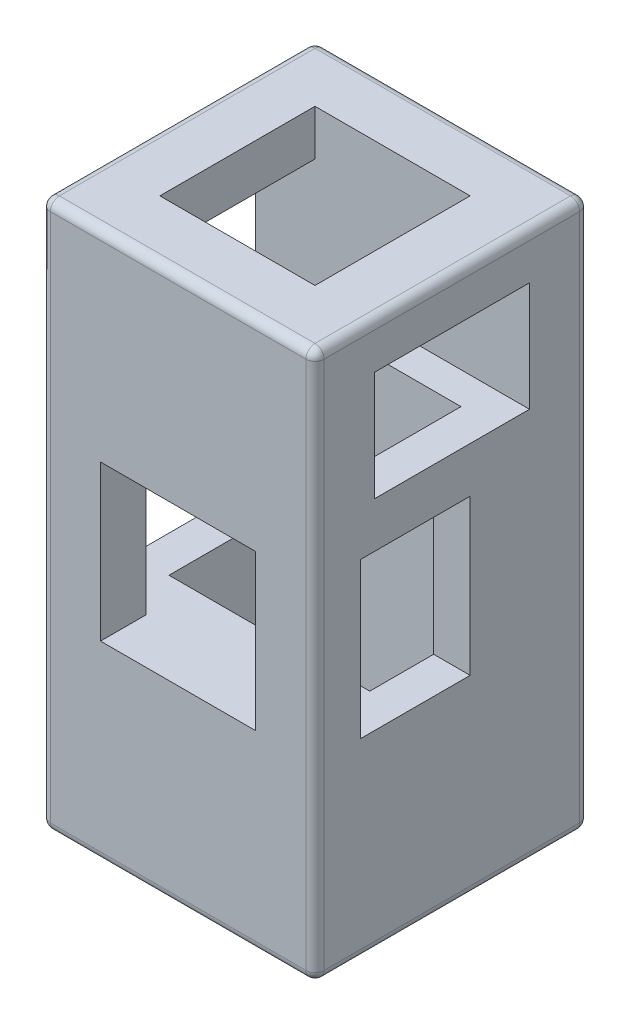
SolidWorks part; units mm, degrees
ref_plane "正面" through (0, 0, 0) normal (0, 0, 1) x (1, 0, 0)
ref_plane "平面" through (0, 0, 0) normal (0, 1, 0) x (1, 0, 0)
ref_plane "右側面" through (0, 0, 0) normal (1, 0, 0) x (0, 0, -1)
sketch "ｽｹｯﾁ1" plane through (0, 0, 0) normal (0, 1, 0) x (1, 0, 0)
  line L1 (-15, 15) -> (15, 15)
  line L2 (-15, 15) -> (-15, -15)
  line L3 (-15, -15) -> (15, -15)
  line L4 (15, 15) -> (15, -15)
  line L5 (-15, 15) -> (15, -15) construction
  line L6 (-15, -15) -> (15, 15) construction
  point P0 (0, 0)
  dimension "D1" = 30
  dimension "D2" = 30
extrude "ﾎﾞｽ - 押し出し2" add sketch "ｽｹｯﾁ1" along normal blind 60
sketch "ｽｹｯﾁ2" plane through (0, 0, 0) normal (0, -1, 0) x (1, 0, 0)
  line L1 (-11, 5) -> (11, 5)
  line L2 (-11, 5) -> (-11, -5)
  line L3 (-11, -5) -> (11, -5)
  line L4 (11, 5) -> (11, -5)
  line L5 (-11, 5) -> (11, -5) construction
  line L6 (-11, -5) -> (11, 5) construction
  point P0 (0, 0)
  dimension "D1" = 10
  dimension "D2" = 22
extrude "ｶｯﾄ - 押し出し1" cut sketch "ｽｹｯﾁ2" against normal blind 47
sketch "ｽｹｯﾁ3" plane through (15, 0, 0) normal (1, 0, 0) x (0, 0, -1)
  line L0 (-15, 60) -> (-15, 0) construction
  line L1 (-8.5, 43) -> (8.5, 43)
  line L2 (-8.5, 43) -> (-8.5, 55)
  line L3 (-8.5, 55) -> (8.5, 55)
  line L4 (8.5, 43) -> (8.5, 55)
  line L5 (-8.5, 43) -> (8.5, 55) construction
  line L6 (-8.5, 55) -> (8.5, 43) construction
  line L7 (15, 60) -> (-15, 60) construction
  point P0 (0, 49)
  dimension "D1" = 12
  dimension "D2" = 17
  dimension "D3" = 15
  dimension "D4" = 5
extrude "ｶｯﾄ - 押し出し2" cut sketch "ｽｹｯﾁ3" against normal through all
sketch "ｽｹｯﾁ5" plane through (0, 60, 0) normal (0, 1, 0) x (1, 0, 0)
  line L1 (8.5, -8.5) -> (-8.5, -8.5)
  line L2 (8.5, -8.5) -> (8.5, 8.5)
  line L3 (8.5, 8.5) -> (-8.5, 8.5)
  line L4 (-8.5, -8.5) -> (-8.5, 8.5)
  line L5 (8.5, -8.5) -> (-8.5, 8.5) construction
  line L6 (8.5, 8.5) -> (-8.5, -8.5) construction
  point P0 (0, 0)
  dimension "D1" = 17
  dimension "D2" = 17
extrude "ｶｯﾄ - 押し出し3" cut sketch "ｽｹｯﾁ5" against normal blind 5
sketch "ｽｹｯﾁ6" plane through (15, 0, 0) normal (1, 0, 0) x (0, 0, -1)
  line L0 (-15, 60) -> (-15, 0) construction
  line L1 (2, 38) -> (-10, 38)
  line L2 (2, 38) -> (2, 21)
  line L3 (2, 21) -> (-10, 21)
  line L4 (-10, 38) -> (-10, 21)
  line L5 (2, 38) -> (-10, 21) construction
  line L6 (2, 21) -> (-10, 38) construction
  line L7 (-8.5, 43) -> (8.5, 43) construction
  point P0 (-4, 29.5)
  dimension "D1" = 17
  dimension "D2" = 12
  dimension "D3" = 5
  dimension "D4" = 5
extrude "ｶｯﾄ - 押し出し4" cut sketch "ｽｹｯﾁ6" against normal through all
sketch "ｽｹｯﾁ7" plane through (0, 0, 15) normal (0, 0, 1) x (1, 0, 0)
  line L0 (15, 60) -> (15, 0) construction
  line L1 (-8.5, 38) -> (8.5, 38)
  line L2 (-8.5, 38) -> (-8.5, 21)
  line L3 (-8.5, 21) -> (8.5, 21)
  line L4 (8.5, 38) -> (8.5, 21)
  line L5 (-8.5, 38) -> (8.5, 21) construction
  line L6 (-8.5, 21) -> (8.5, 38) construction
  line L8 (-15, 60) -> (15, 60) construction
  point P0 (0, 29.5)
  dimension "D1" = 17
  dimension "D2" = 17
  dimension "D3" = 15
  dimension "D4" = 22
extrude "ｶｯﾄ - 押し出し5" cut sketch "ｽｹｯﾁ7" against normal blind 5
fillet "ﾌｨﾚｯﾄ1" radius 1 1 edges at (15, 30, 15)
fillet "ﾌｨﾚｯﾄ2" radius 1 3 edges at (15, 0, -0.5) (14.7071, 0, 14.7071) (-0.5, 0, 15)
fillet "ﾌｨﾚｯﾄ3" radius 1 3 edges at (15, 30.5, -15) (14.7071, 0.2929, -15) (-0.5, 0, -15)
fillet "ﾌｨﾚｯﾄ4" radius 1 5 edges at (-0.5, 60, 15) (14.7071, 60, 14.7071) (-0.5, 60, -15) (14.7071, 60, -14.7071) (15, 60, 0)
fillet "ﾌｨﾚｯﾄ5" radius 1 8 edges at (-15, 59.7071, 14.7071) (-15, 60, 0) (-15, 59.7071, -14.7071) (-15, 30, -15) (-15, 0.2929, -14.7071) (-15, 0, 0) (-15, 0.2929, 14.7071) (-15, 30, 15)
